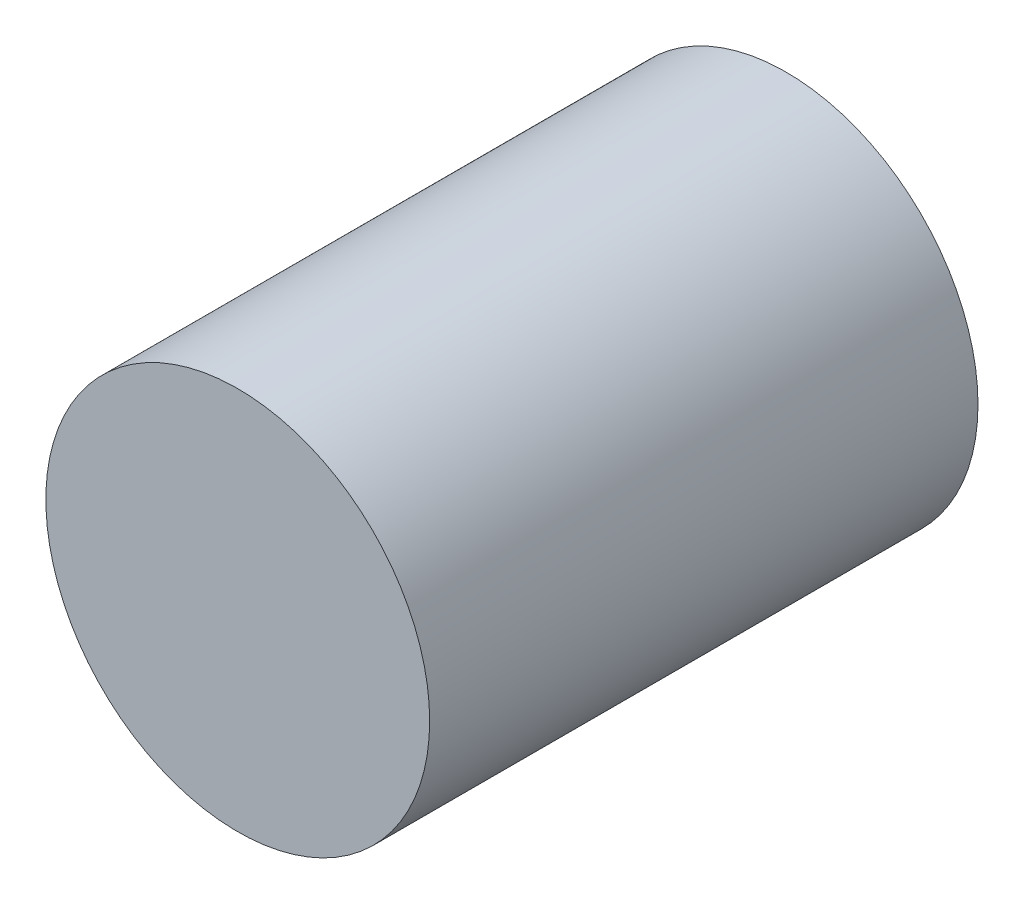
SolidWorks part; units mm, degrees
ref_plane "前视基准面" through (0, 0, 0) normal (0, 0, 1) x (1, 0, 0)
ref_plane "上视基准面" through (0, 0, 0) normal (0, 1, 0) x (1, 0, 0)
ref_plane "右视基准面" through (0, 0, 0) normal (1, 0, 0) x (0, 0, -1)
sketch "草图1" plane through (0, 0, 0) normal (0, 0, 1) x (1, 0, 0)
  circle A0 centre (0, 0) radius 140
  dimension "D1" = 280
extrude "凸台-拉伸1" add sketch "草图1" along normal blind 400
